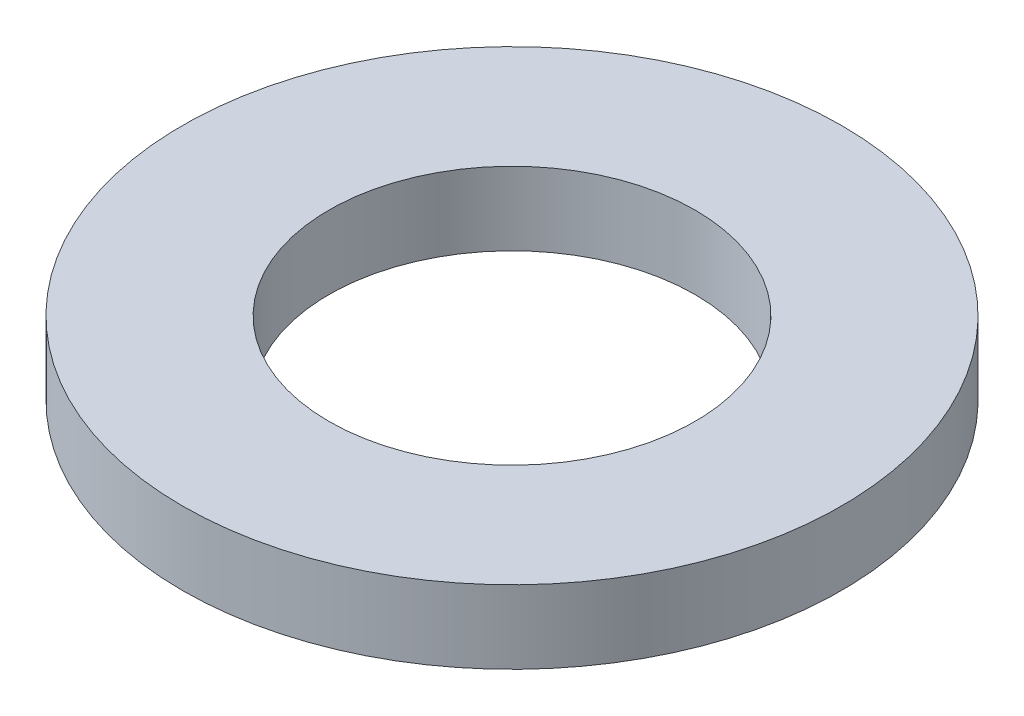
SolidWorks part; units mm, degrees
ref_plane "Front Plane" through (0, 0, 0) normal (0, 0, 1) x (1, 0, 0)
ref_plane "Top Plane" through (0, 0, 0) normal (0, 1, 0) x (1, 0, 0)
ref_plane "Right Plane" through (0, 0, 0) normal (1, 0, 0) x (0, 0, -1)
sketch "Sketch1" plane through (0, 0, 0) normal (0, 1, 0) x (1, 0, 0)
  circle A0 centre (0, 0) radius 25
  circle A1 centre (0, 0) radius 45
extrude "Boss-Extrude1" add sketch "Sketch1" along normal blind 10
